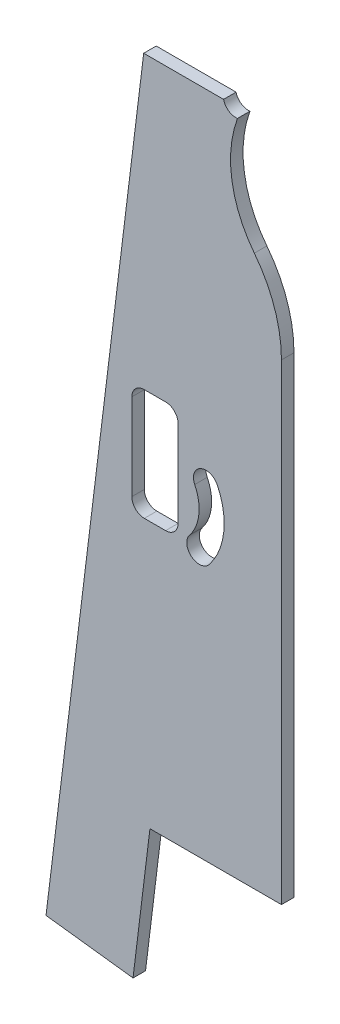
SolidWorks part; units mm, degrees
ref_plane "Front Plane" through (0, 0, 0) normal (0, 0, 1) x (1, 0, 0)
ref_plane "Top Plane" through (0, 0, 0) normal (0, 1, 0) x (1, 0, 0)
ref_plane "Right Plane" through (0, 0, 0) normal (1, 0, 0) x (0, 0, -1)
sketch "Sketch1" plane through (0, 0, 0) normal (0, 0, 1) x (1, 0, 0)
  line L0 (20.5051, 25.8971) -> (-23.6135, 31.3142)
  line L1 (20.5051, 25.8971) -> (70.0328, 429.2678) construction
  line L2 (-23.6135, 31.3142) -> (25.9142, 434.6849)
  line L3 (95.7642, 95.7471) -> (29.0816, 95.7471)
  line L4 (65.8872, -89.4093) -> (336.2328, -89.4093) construction
  line L5 (291.7277, 345.7849) -> (-86.6189, 345.7849) construction
  line L6 (95.7642, 95.7471) -> (95.7642, 434.6849)
  line L7 (29.0816, 95.7471) -> (20.5051, 25.8971)
  line L11 (25.9142, 434.6849) -> (95.7642, 434.6849)
  point P4 (14.9986, 345.7849)
  dimension "D1" = 406.4
  dimension "D2" = 44.45
  dimension "D3" = 83
  dimension "D4" = 88.9
  dimension "D5" = 69.85
extrude "Boss-Extrude1" add sketch "Sketch1" along normal blind 6.35
sketch "Sketch2" plane through (0, 0, 6.35) normal (0, 0, 1) x (1, 0, 0)
  circle A0 centre (72.5949, 436.1354) radius 6.35
  dimension "D1" = 12.7
extrude "Cut-Extrude1" cut sketch "Sketch2" against normal blind 6.35
sketch "Sketch3" plane through (0, 0, 6.35) normal (0, 0, 1) x (1, 0, 0)
  line L0 (20.5051, 25.8971) -> (-0.811, 78.5167) construction
  line L1 (31.7892, 248.5426) -> (63.9088, 244.9506) construction
  line L2 (31.7892, 248.5426) -> (54.1098, 230.7011) construction
  line L3 (31.7892, 248.5426) -> (57.4997, 261.0126) construction
  arc A0 (57.4997, 261.0126) -> (54.1098, 230.7011) centre (31.7892, 248.5426) cw construction
  arc A1 (59.07, 226.7363) -> (63.2131, 263.7838) centre (31.7892, 248.5426) ccw
  arc A2 (49.1497, 234.6659) -> (51.7862, 258.2415) centre (31.7892, 248.5426) ccw
  arc A3 (49.1497, 234.6659) -> (59.07, 226.7363) centre (54.1098, 230.7011) ccw
  arc A4 (63.2131, 263.7838) -> (51.7862, 258.2415) centre (57.4997, 261.0126) ccw
  point P6 (60.1871, 245.3668)
  point P9 (60.1871, 245.3668)
  dimension "D4" = 6.35
  dimension "D1" = 28.575
  dimension "D2" = 28.575
  dimension "D3" = 15.875
extrude "Cut-Extrude3" cut sketch "Sketch3" against normal blind 6.35 contours A1 A4 A2 A3
sketch "Sketch4" plane through (0, 0, 6.35) normal (0, 0, 1) x (1, 0, 0)
  line L0 (20.5051, 25.8971) -> (79.1489, 503.5123) construction
  line L1 (74.295, 431.9433) -> (82.0162, 440.3614)
  line L2 (82.0162, 440.3614) -> (105.9899, 438.1646)
  line L3 (95.7642, 334.936) -> (105.9899, 438.1646)
  arc A0 (74.295, 431.9433) -> (82.0162, 374.944) centre (127.0947, 410.073) ccw construction
  arc A1 (82.0162, 374.944) -> (95.7642, 334.936) centre (30.6767, 334.936) cw
  arc A2 (74.295, 431.9433) -> (82.0162, 374.944) centre (127.0947, 410.073) ccw
extrude "Cut-Extrude4" cut sketch "Sketch4" against normal blind 6.35
sketch "Sketch5" plane through (0, 0, 6.35) normal (0, 0, 1) x (1, 0, 0)
  line L0 (21.4692, 279.1826) -> (21.4692, 238.5426) construction
  line L1 (26.2317, 287.1201) -> (37.0267, 287.1201)
  line L2 (19.8817, 280.7701) -> (19.8817, 236.9551)
  line L3 (26.2317, 230.6051) -> (37.0267, 230.6051)
  line L4 (43.3767, 280.7701) -> (43.3767, 236.9551)
  line L5 (41.7892, 240.0426) -> (41.7892, 277.0426) construction
  line L6 (41.7892, 279.1826) -> (21.4692, 279.1826) construction
  line L7 (40.2892, 238.5426) -> (23.2892, 238.5426) construction
  arc A0 (37.0267, 230.6051) -> (43.3767, 236.9551) centre (37.0267, 236.9551) ccw
  arc A1 (19.8817, 236.9551) -> (26.2317, 230.6051) centre (26.2317, 236.9551) ccw
  arc A2 (26.2317, 287.1201) -> (19.8817, 280.7701) centre (26.2317, 280.7701) ccw
  arc A3 (37.0267, 287.1201) -> (43.3767, 280.7701) centre (37.0267, 280.7701) cw
  dimension "D5" = 6.35
  dimension "D1" = 1.5875
  dimension "D2" = 1.5875
  dimension "D3" = 7.9375
  dimension "D4" = 7.9375
extrude "Cut-Extrude6" cut sketch "Sketch5" against normal blind 6.35 contours A2 L2 A1 L3 A0 L4 A3 L1
